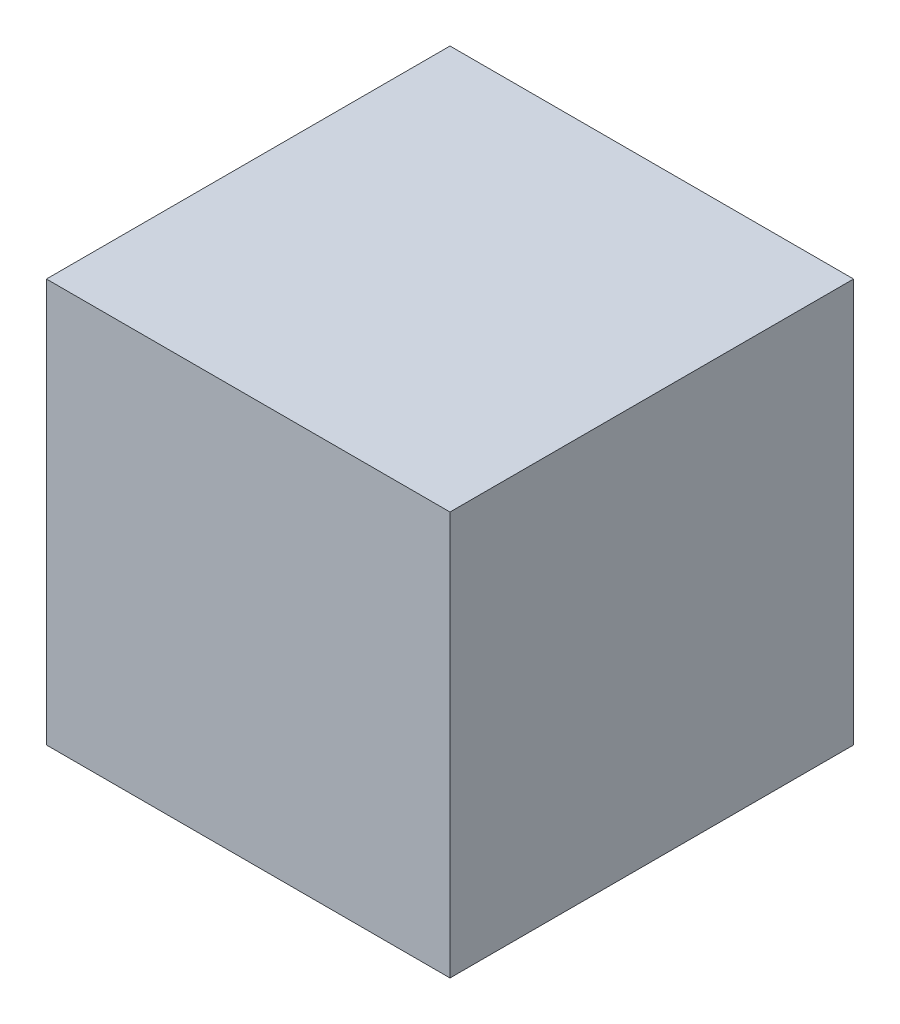
SolidWorks part; units mm, degrees
ref_plane "前视基准面" through (0, 0, 0) normal (0, 0, 1) x (1, 0, 0)
ref_plane "上视基准面" through (0, 0, 0) normal (0, 1, 0) x (1, 0, 0)
ref_plane "右视基准面" through (0, 0, 0) normal (1, 0, 0) x (0, 0, -1)
other "Configuration Table"
sketch "Sketch1" plane through (0, 0, 0) normal (0, 0, 1) x (1, 0, 0)
  line L1 (0, 0) -> (-23, 0)
  line L2 (0, 0) -> (0, 23)
  line L3 (0, 23) -> (-23, 23)
  line L4 (-23, 0) -> (-23, 23)
  dimension "D1" = 23
  dimension "D2" = 23
extrude "Boss-Extrude1" add sketch "Sketch1" along normal blind 23
